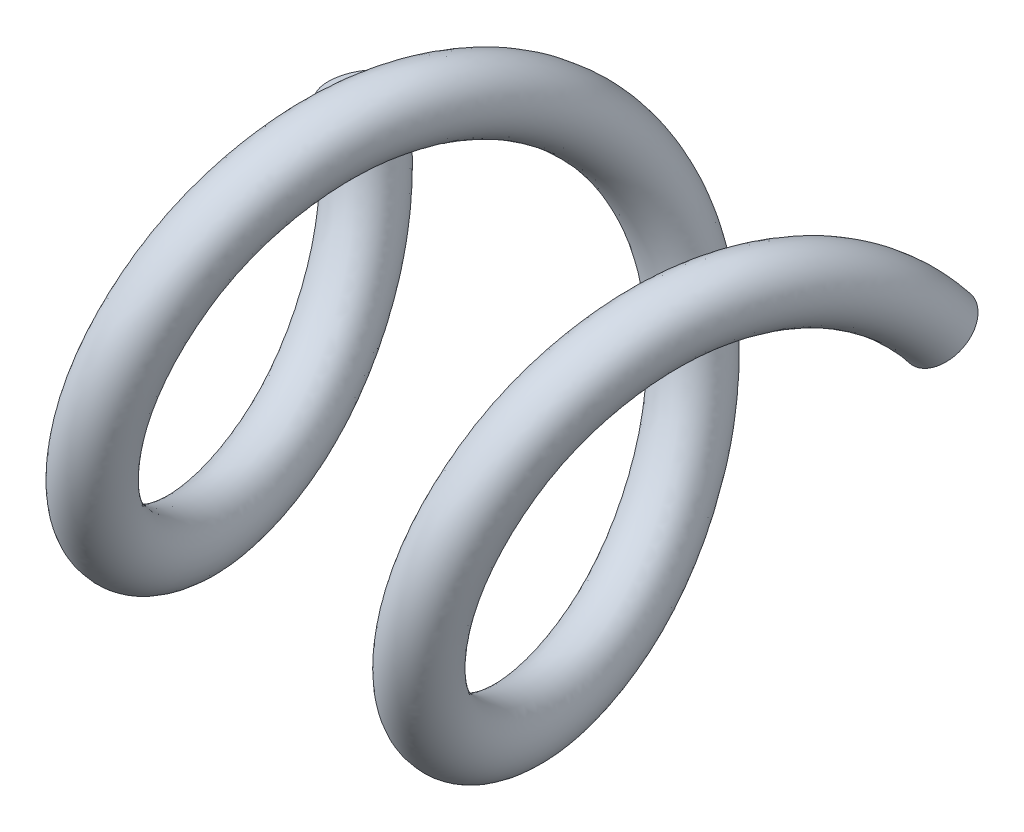
SolidWorks part; units mm, degrees
material "AISI 1015 Steel, Cold Drawn (SS)"
ref_plane "Front Plane" through (0, 0, 0) normal (0, 0, 1) x (1, 0, 0)
ref_plane "Top Plane" through (0, 0, 0) normal (0, 1, 0) x (1, 0, 0)
ref_plane "Right Plane" through (0, 0, 0) normal (1, 0, 0) x (0, 0, -1)
sketch "Sketch1" plane through (0, 0, 0) normal (1, 0, 0) x (0, 0, -1)
  circle A0 centre (0, 0) radius 1.3
  dimension "D1" = 2.6
curve "Helix/Spiral1" pitch 2 height 3.8 turns 1.9
ref_plane "Plane1" through (3.8, 0.7641, -1.0517) normal (0.2378, -0.7858, -0.5709) x (-0.9579, -0.287, -0.004)
sketch "Sketch2" plane through (3.8, 0.7641, -1.0517) normal (0.2378, -0.7858, -0.5709) x (-0.9579, -0.287, -0.004)
  circle A0 centre (0, 0) radius 0.2
  dimension "D1" = 0.4
sweep "Sweep1" add profiles "Sketch2" path "Helix/Spiral1"
